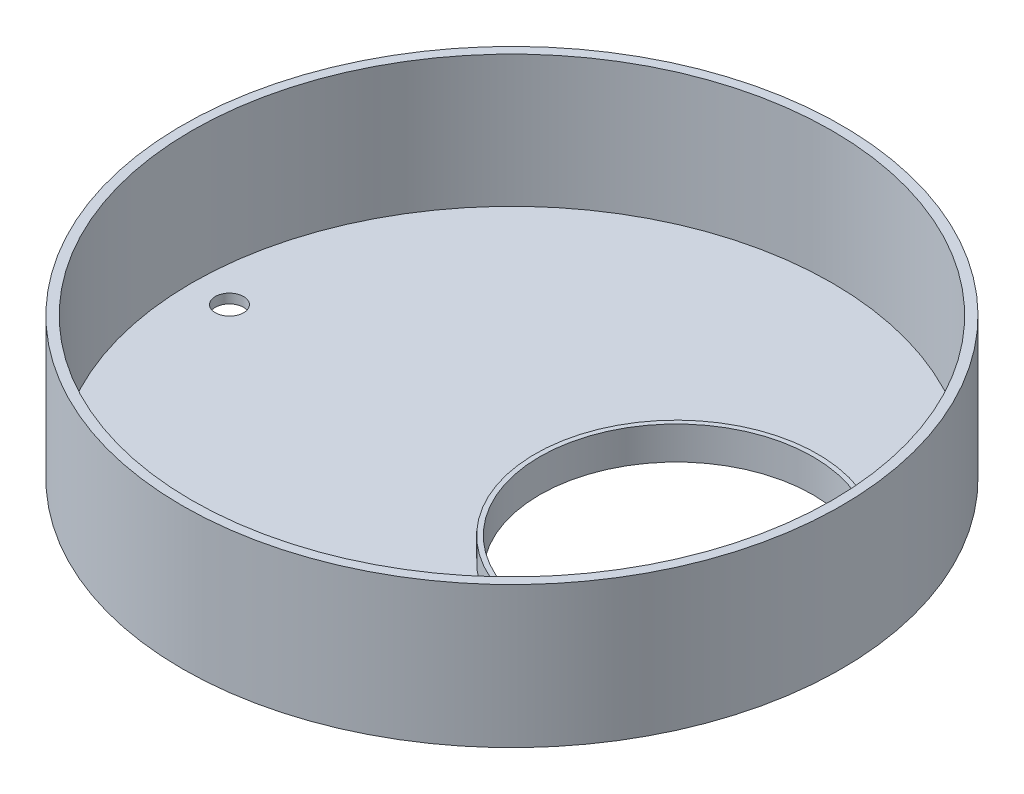
SolidWorks part; units mm, degrees
ref_plane "Front Plane" through (0, 0, 0) normal (0, 0, 1) x (1, 0, 0)
ref_plane "Top Plane" through (0, 0, 0) normal (0, 1, 0) x (1, 0, 0)
ref_plane "Right Plane" through (0, 0, 0) normal (1, 0, 0) x (0, 0, -1)
sketch "Sketch1" plane through (0, 0, 0) normal (0, 1, 0) x (1, 0, 0)
  circle A0 centre (0, 0) radius 70
  dimension "D1" = 140
extrude "Boss-Extrude1" add sketch "Sketch1" along normal blind 30
shell "Shell1" thickness 2
sketch "Sketch2" plane through (0, 2, 0) normal (0, 1, 0) x (1, 0, 0)
  line L0 (0, 0) -> (68, 0) construction
  circle A0 centre (34.9213, 0) radius 29
  dimension "D1" = 58
extrude "Extrude-Thin1" add sketch "Sketch2" along normal blind 5 thin
sketch "Sketch3" plane through (0, 7, 0) normal (0, 1, 0) x (1, 0, 0)
  circle A1 centre (34.9213, 0) radius 33
  circle A3 centre (34.9213, 0) radius 30
  dimension "D1" = 66
  dimension "D2" = 60
extrude "Cut-Extrude1" cut sketch "Sketch3" against normal blind 5
sketch "Sketch4" plane through (0, 2, 0) normal (0, 1, 0) x (1, 0, 0)
  circle A0 centre (34.9213, 0) radius 29
  circle A1 centre (34.9213, 0) radius 30 construction
extrude "Cut-Extrude2" cut sketch "Sketch4" against normal blind 2
sketch "Sketch5" plane through (0, 2, 0) normal (0, 1, 0) x (1, 0, 0)
  circle A0 centre (-60, 0) radius 3
  dimension "D1" = 6
  dimension "D2" = 60
extrude "Cut-Extrude3" cut sketch "Sketch5" against normal mid plane 10
